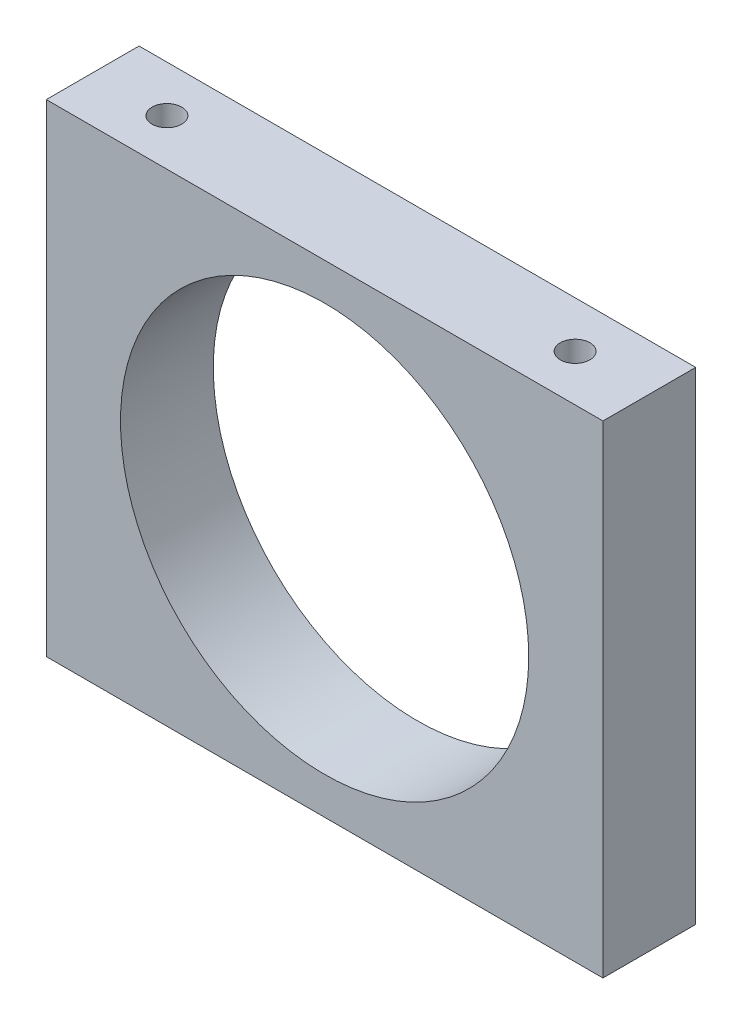
SolidWorks part; units mm, degrees
ref_plane "Plan de face" through (0, 0, 0) normal (0, 0, 1) x (1, 0, 0)
ref_plane "Plan de dessus" through (0, 0, 0) normal (0, 1, 0) x (1, 0, 0)
ref_plane "Plan de droite" through (0, 0, 0) normal (1, 0, 0) x (0, 0, -1)
sketch "Esquisse1" plane through (0, 0, 0) normal (0, 0, 1) x (1, 0, 0)
  line L1 (0, 0) -> (30, 0)
  line L2 (0, 0) -> (0, 26)
  line L3 (0, 26) -> (30, 26)
  line L4 (30, 0) -> (30, 26)
  circle A0 centre (15, 13) radius 11
  dimension "D3" = 22
  dimension "D1" = 26
  dimension "D2" = 30
  dimension "D4" = 15
  dimension "D5" = 13
extrude "Boss.-Extru.1" add sketch "Esquisse1" along normal blind 5
hole_wizard "Trou pour taraudage pour trou taraudé M21" positions "Esquisse2" profile "Esquisse3" hole size "M2" standard "ISO"
sketch "Esquisse2" plane through (0, 26, 0) normal (0, 1, 0) x (1, 0, 0)
  line L0 (0, -5) -> (0, 0) construction
  line L1 (30, -5) -> (30, 0) construction
  line L2 (30, 0) -> (0, 0) construction
  point P0 (4, -2.5)
  point P2 (26, -2.5)
  dimension "D1" = 4
  dimension "D2" = 4
  dimension "D3" = 2.5
  dimension "D4" = 2.5
sketch "Esquisse3" plane through (4, 26, 2.5) normal (1, 0, 0) x (0, 0, 1)
  line L0 (0, 0) -> (0, 5.4807)
  line L1 (0, 5.4807) -> (0.8, 5)
  line L2 (0.8, 5) -> (0.8, 0)
  line L5 (0.8, 0) -> (0, 0)
  line L10 (0, 5.4807) -> (-0.8, 5) construction
  line L11 (0, -6.35) -> (0, 107.95) construction
  dimension "Diamètre du perçage" = 1.6
  dimension "Profondeur du perçage" = 5
  dimension "Angle de pointe" = 118
hole_wizard "Trou pour taraudage pour trou taraudé M22" positions "Esquisse4" profile "Esquisse5" hole size "M2" standard "ISO"
sketch "Esquisse4" plane through (0, 0, 0) normal (0, -1, 0) x (-1, 0, 0)
  line L0 (-30, -5) -> (-30, 0) construction
  line L1 (0, -5) -> (0, 0) construction
  line L2 (0, 0) -> (-30, 0) construction
  point P0 (-4, -2.5)
  point P2 (-26, -2.5)
  dimension "D1" = 4
  dimension "D2" = 4
  dimension "D3" = 2.5
  dimension "D4" = 2.5
sketch "Esquisse5" plane through (4, 0, 2.5) normal (1, 0, 0) x (0, 0, -1)
  line L0 (0, 0) -> (0, 5.4807)
  line L1 (0, 5.4807) -> (0.8, 5)
  line L2 (0.8, 5) -> (0.8, 0)
  line L5 (0.8, 0) -> (0, 0)
  line L10 (0, 5.4807) -> (-0.8, 5) construction
  line L11 (0, -6.35) -> (0, 107.95) construction
  dimension "Diamètre du perçage" = 1.6
  dimension "Profondeur du perçage" = 5
  dimension "Angle de pointe" = 118
equation "\"D4@Esquisse1\"=\"D2@Esquisse1\"/2"
equation "\"D5@Esquisse1\"=\"D1@Esquisse1\"/2"
equation "\"D3@Esquisse2\"=\"D1@Boss.-Extru.1\"/2"
equation "\"D4@Esquisse2\"=\"D1@Boss.-Extru.1\"/2"
equation "\"D3@Esquisse4\"=\"D1@Boss.-Extru.1\"/2"
equation "\"D4@Esquisse4\"=\"D1@Boss.-Extru.1\"/2"
